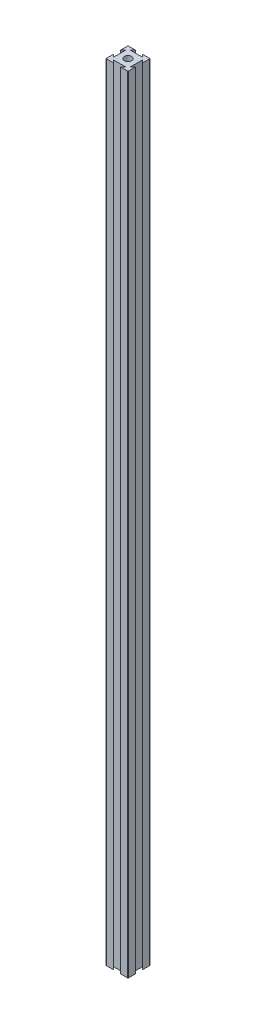
SolidWorks part; units mm, degrees
material "Alumina"
ref_plane "Front Plane" through (0, 0, 0) normal (0, 0, 1) x (1, 0, 0)
ref_plane "Top Plane" through (0, 0, 0) normal (0, 1, 0) x (1, 0, 0)
ref_plane "Right Plane" through (0, 0, 0) normal (1, 0, 0) x (0, 0, -1)
sketch "Sketch1" plane through (0, 0, 0) normal (0, 1, 0) x (1, 0, 0)
  line L0 (6.6667, 20) -> (4.285, 17.6183)
  line L1 (0, 0) -> (20, 0)
  line L2 (0, 0) -> (0, 20)
  line L3 (0, 20) -> (20, 20)
  line L4 (20, 0) -> (20, 20)
  line L5 (4.285, 17.6183) -> (15.715, 17.6183)
  line L6 (15.715, 17.6183) -> (13.3333, 20)
  line L7 (13.3333, 20) -> (6.6667, 20)
  line L8 (0, 10) -> (20, 10) construction
  line L9 (10, 20) -> (10, 0) construction
  line L10 (15.715, 2.3817) -> (13.3333, 0)
  line L11 (4.285, 2.3817) -> (15.715, 2.3817)
  line L12 (6.6667, 0) -> (4.285, 2.3817)
  line L13 (13.3333, 0) -> (6.6667, 0)
  line L14 (0, 13.3333) -> (2.3817, 15.715)
  line L15 (2.3817, 15.715) -> (2.3817, 4.285)
  line L16 (2.3817, 4.285) -> (0, 6.6667)
  line L17 (0, 6.6667) -> (0, 13.3333)
  line L18 (17.6183, 4.285) -> (20, 6.6667)
  line L19 (17.6183, 15.715) -> (17.6183, 4.285)
  line L20 (20, 13.3333) -> (17.6183, 15.715)
  line L21 (20, 6.6667) -> (20, 13.3333)
  circle A0 centre (10, 10) radius 3.3333
  dimension "D1" = 20
  dimension "D2" = 20
  dimension "D3" = 6.6667
  dimension "D4" = 6.6667
  dimension "D5" = 45
  dimension "D6" = 45
  dimension "D7" = 11.43
  dimension "D8" = 6.6667
  dimension "D9" = 6.6667
  dimension "D10" = 11.43
  dimension "D11" = 45
  dimension "D12" = 45
extrude "Boss-Extrude1" add sketch "Sketch1" along normal blind 711.2 contours L20 L4 L3 L6 L5 L0 L2 L14 L15 L16 L1 L12 L11 L10 L18 L19 A0
fillet "Fillet4" radius 0.508 4 edges at (0, 355.6, -20) (20, 355.6, -20) (0, 355.6, 0) (20, 355.6, 0)
